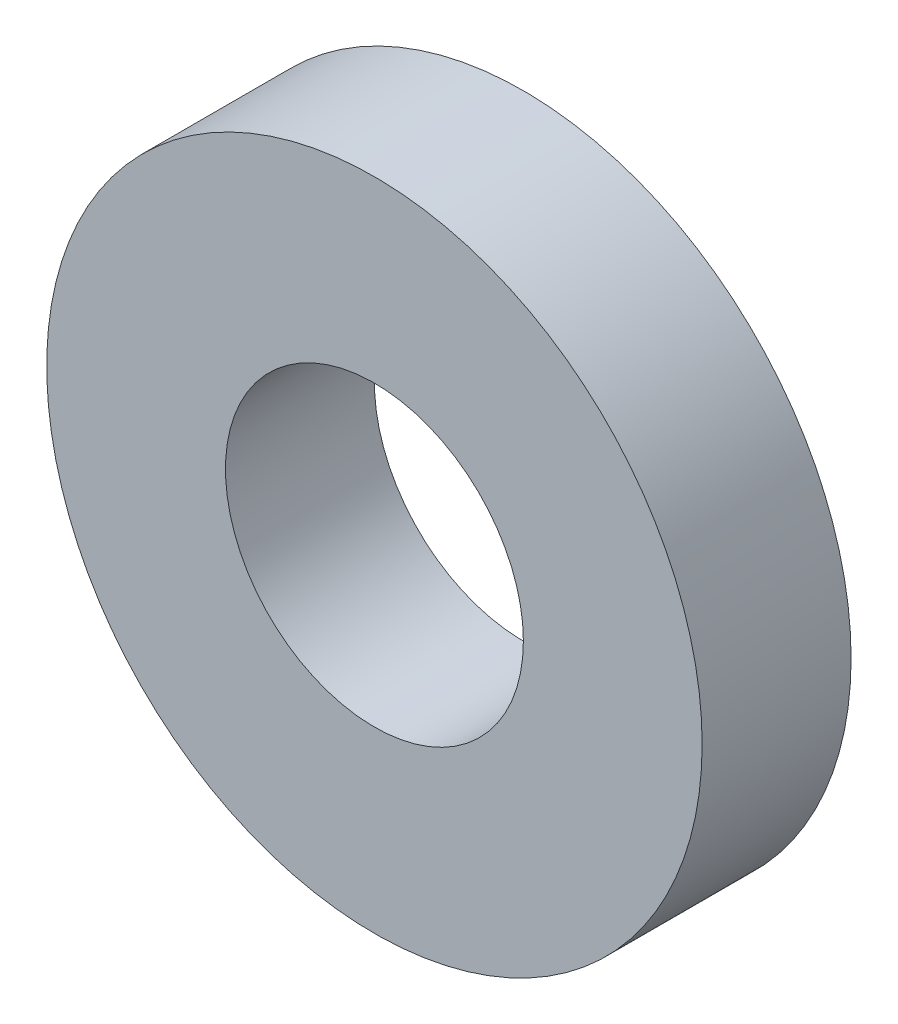
SolidWorks part; units mm, degrees
ref_plane "Front Plane" through (0, 0, 0) normal (0, 0, 1) x (1, 0, 0)
ref_plane "Top Plane" through (0, 0, 0) normal (0, 1, 0) x (1, 0, 0)
ref_plane "Right Plane" through (0, 0, 0) normal (1, 0, 0) x (0, 0, -1)
sketch "Sketch1" plane through (0, 0, 0) normal (0, 0, 1) x (1, 0, 0)
  circle A0 centre (0, 0) radius 6
  circle A1 centre (0, 0) radius 13.2
extrude "Boss-Extrude1" add sketch "Sketch1" along normal blind 6
sketch "Sketch2" plane through (0, 0, 6) normal (0, 0, 1) x (1, 0, 0)
  line L0 (0, 0) -> (0, 15.2) construction
  line L1 (-1.8199, 15.2) -> (0, 0) construction
  line L2 (1.8199, 15.2) -> (0, 0) construction
  arc A0 (-0.8428, 7.0392) -> (0.8428, 7.0392) centre (0, 0) cw
  arc A1 (-2.8199, 12.8953) -> (2.8199, 12.8953) centre (0, 0) cw
  arc A2 (-1.8199, 10.32) -> (1.8199, 10.32) centre (0, 0) cw
  arc A3 (-2.8199, 12.8953) -> (-1.8199, 10.32) centre (-37.9293, -2.2197) ccw
  arc A4 (2.8199, 12.8953) -> (1.8199, 10.32) centre (37.9293, -2.2197) cw
  point P7 (0, 7.0894)
sketch "Sketch3" plane through (0, 0, 0) normal (0, 0, 1) x (1, 0, 0)
  circle A0 centre (0, 0) radius 6
  circle A1 centre (0, 0) radius 13.2
extrude "Boss-Extrude2" add sketch "Sketch3" along normal blind 6
